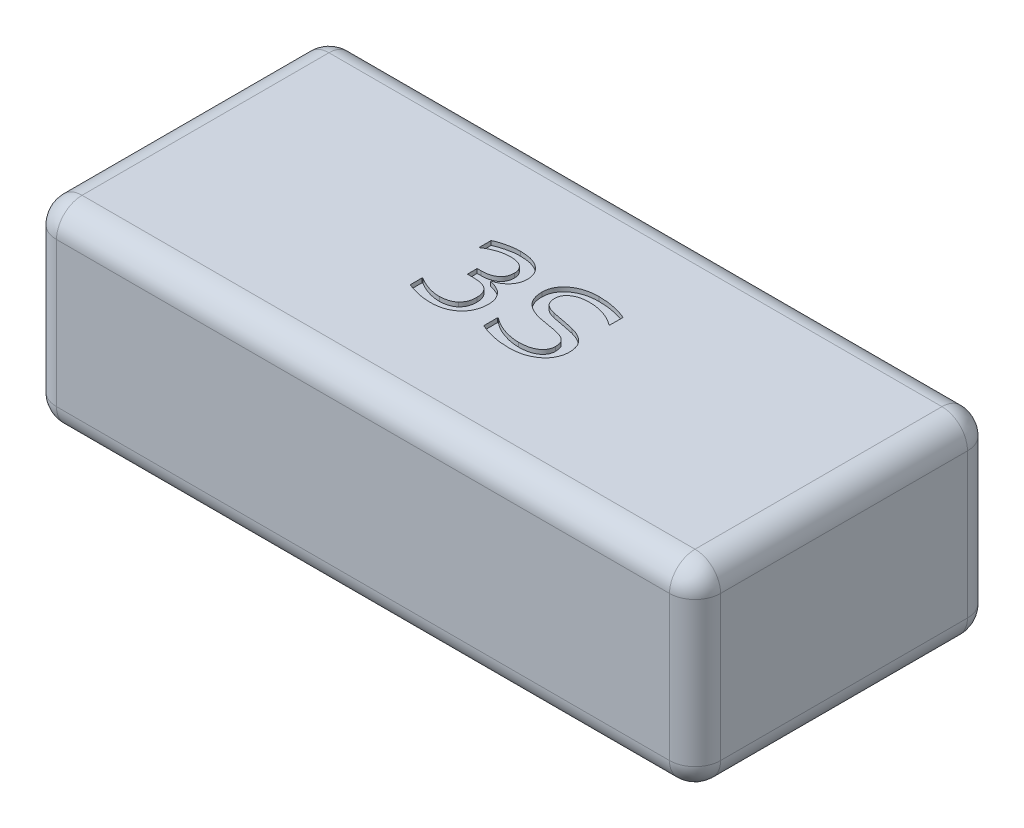
SolidWorks part; units mm, degrees
material "uhlíková ocel 7850"
ref_plane "Přední rovina" through (0, 0, 0) normal (0, 0, 1) x (1, 0, 0)
ref_plane "Horní rovina" through (0, 0, 0) normal (0, 1, 0) x (1, 0, 0)
ref_plane "Pravá rovina" through (0, 0, 0) normal (1, 0, 0) x (0, 0, -1)
sketch "Skica1" plane through (0, 0, 0) normal (0, 1, 0) x (1, 0, 0)
  line L1 (39, -17.5) -> (-39, -17.5)
  line L2 (39, -17.5) -> (39, 17.5)
  line L3 (39, 17.5) -> (-39, 17.5)
  line L4 (-39, -17.5) -> (-39, 17.5)
  line L5 (39, -17.5) -> (-39, 17.5) construction
  line L6 (39, 17.5) -> (-39, -17.5) construction
  point P0 (0, 0)
  dimension "D1" = 35
  dimension "D2" = 78
extrude "Přidat vysunutím1" add sketch "Skica1" along normal blind 23
fillet "Zaoblit1" radius 3 12 edges at (-39, 11.5, -17.5) (39, 11.5, -17.5) (-39, 11.5, 17.5) (39, 11.5, 17.5) (0, 0, 17.5) (39, 0, 0) (0, 0, -17.5) (-39, 0, 0) (0, 23, -17.5) (39, 23, 0) (0, 23, 17.5) (-39, 23, 0)
sketch "Skica2" plane through (0, 23, 0) normal (0, 1, 0) x (1, 0, 0)
  text T0 "3S" font "Verdana" height 10
extrude "Odebrat vysunutím1" cut sketch "Skica2" against normal blind 0.5
